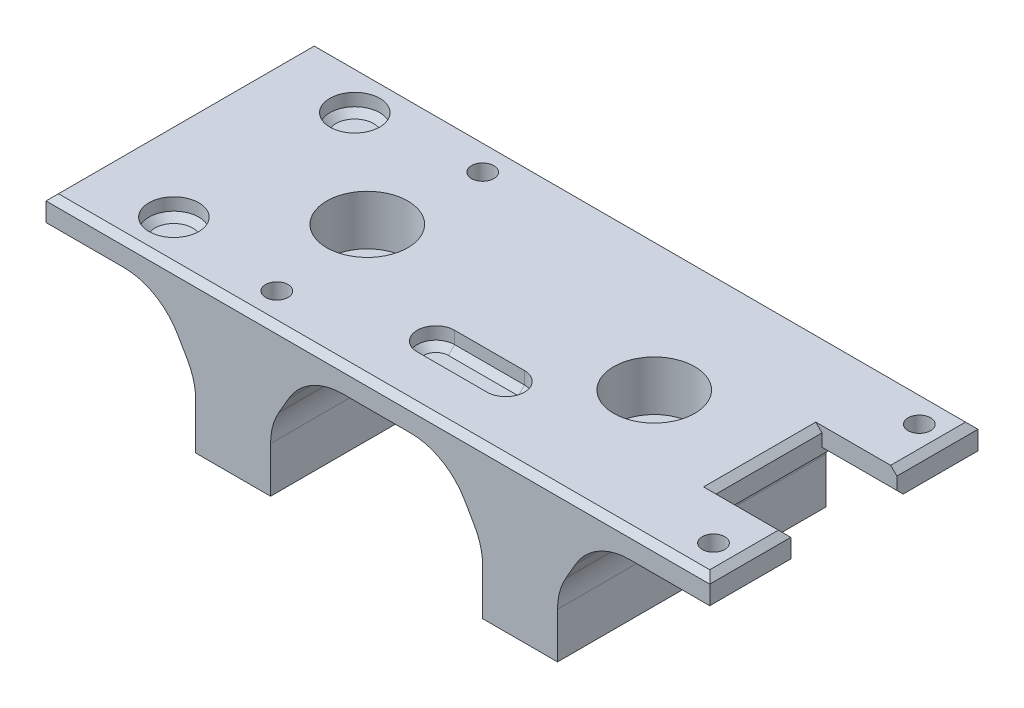
SolidWorks part; units mm, degrees
ref_plane "Front Plane" through (0, 0, 0) normal (0, 0, 1) x (1, 0, 0)
ref_plane "Top Plane" through (0, 0, 0) normal (0, 1, 0) x (1, 0, 0)
ref_plane "Right Plane" through (0, 0, 0) normal (1, 0, 0) x (0, 0, -1)
sketch "Sketch1" plane through (0, 0, 0) normal (0, 1, 0) x (1, 0, 0)
  line L5 (-26.6, -10.75) -> (26.6, -10.75)
  line L6 (-26.6, -10.75) -> (-26.6, 10.75)
  line L7 (-26.6, 10.75) -> (26.6, 10.75)
  line L8 (26.6, -10.75) -> (26.6, 10.75)
  line L9 (-26.6, -10.75) -> (26.6, 10.75) construction
  line L10 (-26.6, 10.75) -> (26.6, -10.75) construction
  point P0 (0, 0)
  dimension "D1" = 53.2
  dimension "D2" = 21.5
extrude "Boss-Extrude1" add sketch "Sketch1" along normal blind 12
sketch "Sketch2" plane through (0, 12, 0) normal (0, 1, 0) x (1, 0, 0)
  line L0 (26.6, -10.75) -> (26.6, 10.75) construction
  line L1 (-10.6, 8.25) -> (24.4, 8.25) construction
  line L2 (-10.6, 8.25) -> (-10.6, -8.25) construction
  line L3 (-10.6, -8.25) -> (24.4, -8.25) construction
  line L4 (24.4, 8.25) -> (24.4, -8.25) construction
  circle A0 centre (24.4, 8.25) radius 0.9
  circle A1 centre (24.4, -8.25) radius 0.9
  circle A2 centre (-10.6, -8.25) radius 0.9
  circle A3 centre (-10.6, 8.25) radius 0.9
  point P8 (24.4, 0)
  dimension "D3" = 1.8
  dimension "D1" = 16.5
  dimension "D2" = 35
  dimension "D4" = 2.2
extrude "Cut-Extrude1" cut sketch "Sketch2" against normal blind 5
sketch "Sketch3" plane through (0, 0, 0) normal (0, -1, 0) x (1, 0, 0)
  line L0 (26.6, 10.75) -> (26.6, -10.75) construction
  line L1 (26.6, 4.25) -> (20.6, 4.25)
  line L2 (26.6, 4.25) -> (26.6, -4.25)
  line L3 (26.6, -4.25) -> (20.6, -4.25)
  line L4 (20.6, 4.25) -> (20.6, -4.25)
  point P6 (20.6, 0)
  dimension "D1" = 8.5
  dimension "D2" = 6
extrude "Cut-Extrude2" cut sketch "Sketch3" against normal through all
sketch "Sketch5" plane through (0, 12, 0) normal (0, 1, 0) x (1, 0, 0)
  line L0 (-0.75, -5.35) -> (4.85, -5.35) construction
  line L1 (-0.75, -3.85) -> (4.85, -3.85)
  line L2 (-0.75, -6.85) -> (4.85, -6.85)
  line L5 (-19.85, -7.25) -> (-19.85, 7.25) construction
  line L6 (-13.1, 10.75) -> (-26.6, 10.75) construction
  line L7 (-26.6, -10.75) -> (26.6, -10.75) construction
  line L8 (26.6, -10.75) -> (26.6, -4.25) construction
  arc A0 (-0.75, -3.85) -> (-0.75, -6.85) centre (-0.75, -5.35) ccw
  arc A1 (4.85, -6.85) -> (4.85, -3.85) centre (4.85, -5.35) ccw
  circle A2 centre (-19.85, 7.25) radius 2
  circle A3 centre (-19.85, -7.25) radius 2
  point P2 (2.05, -5.35)
  point P14 (-19.85, 0)
  point P20 (-19.85, 10.75)
  dimension "D4" = 1.5
  dimension "D7" = 4
  dimension "D1" = 21.75
  dimension "D2" = 5.6
  dimension "D3" = 5.4
  dimension "D5" = 14.5
  dimension "D6" = 13.5
extrude "Cut-Extrude3" cut sketch "Sketch5" against normal blind 1.5
sketch "Sketch7" plane through (0, 12, 0) normal (0, 1, 0) x (1, 0, 0)
  line L0 (-26.6, 0) -> (20.6, 0) construction
  line L1 (-26.6, 10.75) -> (-26.6, -10.75) construction
  line L2 (20.6, -4.25) -> (20.6, 4.25) construction
  circle A0 centre (-11.6, 0) radius 2.5
  circle A1 centre (11.4, 0) radius 2.5
  dimension "D1" = 5
  dimension "D2" = 15
  dimension "D3" = 38
hole_wizard "CBORE for M3 Cheese Head Screw1" positions "3DSketch1" profile "Sketch8" counterbore size "M3" standard "ISO" end condition through all
sketch3d "3DSketch1"
  point P0 (-11.6, 12, 0)
  point P3 (11.4, 12, 0)
sketch "Sketch8" plane through (-11.6, 12, 0) normal (1, 0, 0) x (0, 0, 1)
  line L0 (0, 0) -> (0, 12)
  line L1 (0, 12) -> (1.7, 12)
  line L3 (1.7, 12) -> (1.7, 4)
  line L4 (1.7, 4) -> (3.25, 4)
  line L5 (3.25, 4) -> (3.25, 0)
  line L7 (3.25, 0) -> (0, 0)
  line L11 (0, -6.35) -> (0, 107.95) construction
  dimension "Thru Hole Dia." = 3.4
  dimension "Thru Hole Depth" = 12
  dimension "C'Bore Dia." = 6.5
  dimension "C'Bore Depth" = 4
sketch "Sketch9" plane through (0, 0, 10.75) normal (0, 0, 1) x (1, 0, 0)
  line L1 (-26.6, 12) -> (26.6, 12)
  line L2 (-26.6, 12) -> (-26.6, 0)
  line L3 (-26.6, 0) -> (26.6, 0)
  line L4 (26.6, 12) -> (26.6, 0)
  line L5 (-26.6, 12) -> (26.6, 12)
  line L6 (-26.6, 12) -> (-26.6, 10)
  line L7 (-26.6, 10) -> (26.6, 10)
  line L8 (26.6, 12) -> (26.6, 10)
  line L18 (-11.6, 12) -> (-11.6, 0) construction
  line L19 (11.4, 12) -> (11.4, 0) construction
  line L20 (-17.4868, 10) -> (-14.6, 5)
  line L21 (-14.6, 5) -> (-14.6, 0)
  line L22 (-14.6, 0) -> (-8.6, 0)
  line L23 (-8.6, 0) -> (-8.6, 5)
  line L24 (-8.6, 5) -> (-5.7132, 10)
  line L25 (-14.6, 5) -> (14.4, 5) construction
  line L26 (5.5132, 10) -> (8.4, 5)
  line L27 (8.4, 5) -> (8.4, 0)
  line L28 (8.4, 0) -> (14.4, 0)
  line L29 (14.4, 0) -> (14.4, 5)
  line L30 (14.4, 5) -> (17.2868, 10)
  line L31 (17.2868, 10) -> (5.5132, 10)
  line L32 (-5.7132, 10) -> (-17.4868, 10)
  line M19 (-26.6, 0) -> (26.6, 0)
  line M20 (26.6, 0) -> (26.6, 12)
  dimension "D1" = 2
  dimension "D2" = 6
  dimension "D3" = 15
  dimension "D4" = 38
  dimension "D5" = 6
  dimension "D6" = 30
  dimension "D7" = 5
extrude "Cut-Extrude4" cut sketch "Sketch9" against normal through all contours L21 L20 L7 L2 M19 | L27 L26 L7 L24 L23 M19 | L30 L29 L7 M19 M20
fillet "Fillet1" radius 5 8 edges at (17.2868, 10, 0) (14.4, 5, 0) (8.4, 5, 0) (5.5132, 10, 0) (-5.7132, 10, 0) (-8.6, 5, 0) (-14.6, 5, 0) (-17.4868, 10, 0)
chamfer "Chamfer2" distance 0.5 angle 45 10 edges at (2.05, 10.5, 3.85) (6.35, 10.5, 5.35) (2.05, 10.5, 6.85) (-2.25, 10.5, 5.35) (-19.85, 10.5, -5.25) (-19.85, 10.5, 9.25) (-10.6, 7, 9.15) (-10.6, 7, -7.35) (-11.6, 8, 1.7) (11.4, 8, 1.7)
chamfer "Chamfer3" distance 0.5 angle 45 8 edges at (23.6, 10, -4.25) (20.6, 12, 0) (23.6, 12, 4.25) (26.6, 12, 7.5) (26.6, 12, -7.5) (0, 12, -10.75) (-26.6, 12, 0) (0, 12, 10.75)
